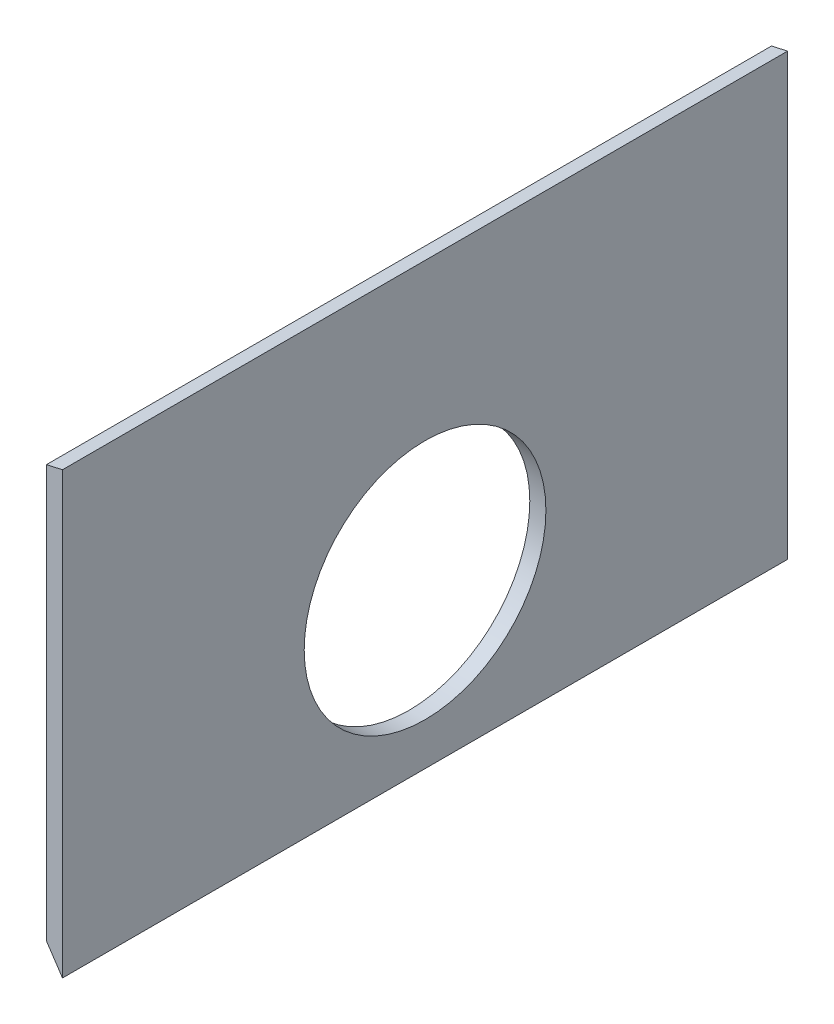
SolidWorks part; units mm, degrees
ref_plane "Ebene vorne" through (0, 0, 0) normal (0, 0, 1) x (1, 0, 0)
ref_plane "Ebene oben" through (0, 0, 0) normal (0, 1, 0) x (1, 0, 0)
ref_plane "Ebene rechts" through (0, 0, 0) normal (1, 0, 0) x (0, 0, -1)
sketch "Skizze1" plane through (0, 0, 0) normal (0, 0, 1) x (1, 0, 0)
  line L0 (331.8583, 76.5237) -> (341.8583, 78.7946)
  line L1 (331.8583, -179.3676) -> (341.8583, -194.3676)
  line L38 (331.8583, 76.5237) -> (331.8583, -179.3676)
  line L39 (341.8583, -194.3676) -> (341.8583, 78.7946)
extrude "Aufsatz-Linear austragen1" add sketch "Skizze1" along normal blind 450
sketch "Skizze2" plane through (331.8583, 0, 0) normal (-1, 0, 0) x (0, 0, 1)
  line L0 (-68.0795, -93.0676) -> (470.0388, -93.0676) construction
  line L1 (225, 132.5785) -> (225, -280.6256) construction
  line L3 (0, 76.5237) -> (0, -179.3676) construction
  line L4 (450, -179.3676) -> (0, -179.3676) construction
  point P8 (225, -93.0676)
  dimension "D1" = 225
  dimension "D2" = 86.3
hole_wizard "Ø15.0 (15) Durchmesser Bohrung1" positions "3D-Skizze1" profile "Skizze4" hole size "Ø15.0" standard "DIN" end condition through all
sketch3d "3D-Skizze1"
  point P0 (331.8583, -93.0676, 225)
sketch "Skizze4" plane through (331.8583, -93.0676, 225) normal (0, 1, 0) x (0, 0, 1)
  line L0 (0, 0) -> (0, 10)
  line L1 (0, 10) -> (75, 10)
  line L2 (75, 10) -> (75, 0)
  line L5 (75, 0) -> (0, 0)
  line L11 (0, -6.35) -> (0, 107.95) construction
  dimension "Bohrerdurchmesser" = 150
  dimension "Bohrungstiefe" = 10
